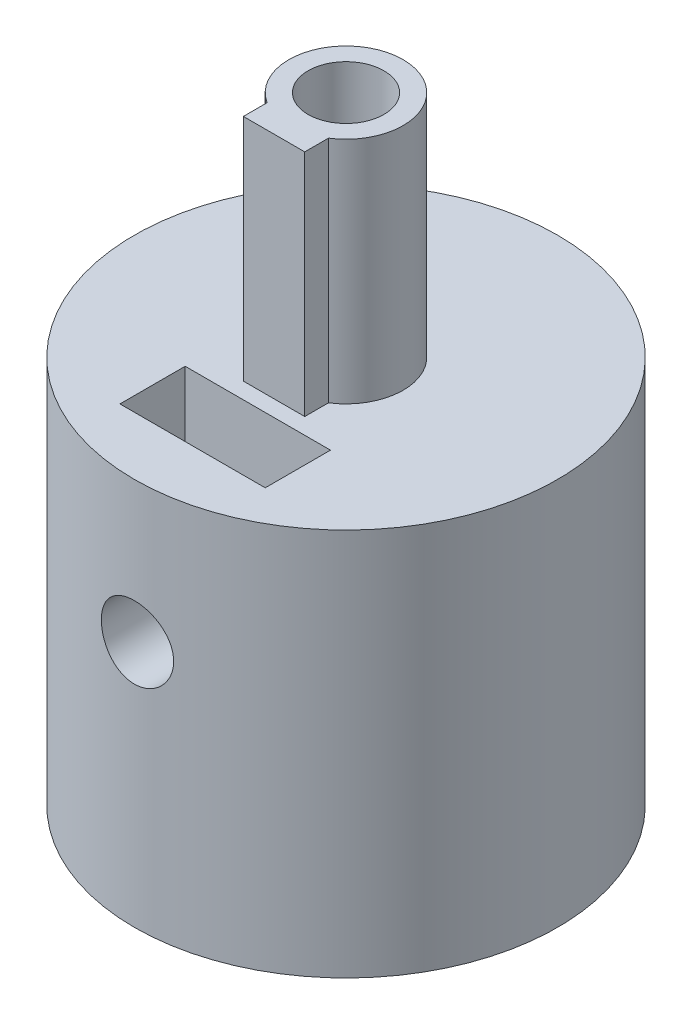
SolidWorks part; units mm, degrees
ref_plane "Front Plane" through (0, 0, 0) normal (0, 0, 1) x (1, 0, 0)
ref_plane "Top Plane" through (0, 0, 0) normal (0, 1, 0) x (1, 0, 0)
ref_plane "Right Plane" through (0, 0, 0) normal (1, 0, 0) x (0, 0, -1)
sketch "Sketch1" plane through (0, 0, 0) normal (0, 1, 0) x (1, 0, 0)
  circle A0 centre (0, 0) radius 1.965 construction
  circle A1 centre (0, 0) radius 6
  dimension "D1" = 3.93
  dimension "D2" = 12
extrude "Boss-Extrude1" add sketch "Sketch1" along normal blind 10
sketch "Sketch2" plane through (0, 0, 0) normal (0, 0, 1) x (1, 0, 0)
  line L0 (0, 10) -> (0, 0) construction
  line L1 (6, 10) -> (-6, 10) construction
  circle A0 centre (0, 7) radius 1.025
  dimension "D1" = 2.05
  dimension "D2" = 3
extrude "Cut-Extrude1" cut sketch "Sketch2" along normal through all
sketch "Sketch4" plane through (0, 0, 0) normal (0, 1, 0) x (1, 0, 0)
  circle A0 centre (0, 0) radius 2.1
  dimension "D1" = 4.2
extrude "Cut-Extrude4" cut sketch "Sketch4" along normal through all
sketch "Sketch5" plane through (0, 10, 0) normal (0, 1, 0) x (1, 0, 0)
  line L0 (-6, 0) -> (6, 0) construction
  line L2 (-0.475, -3.5346) -> (0.475, -3.5346)
  line L3 (-0.475, -3.5346) -> (-0.475, 3.5346)
  line L4 (-0.475, 3.5346) -> (0.475, 3.5346)
  line L5 (0.475, -3.5346) -> (0.475, 3.5346)
  line L6 (0, 3.5346) -> (0, -3.5346) construction
  line L7 (-0.475, 0) -> (0.475, 0) construction
  circle A0 centre (0, 0) radius 6 construction
  point P5 (0, 0)
  dimension "D1" = 0.95
extrude "Boss-Extrude2" add sketch "Sketch5" against normal blind 1.2
sketch "Sketch7" plane through (0, 10, 0) normal (0, 1, 0) x (1, 0, 0)
  circle A0 centre (0, 0) radius 6
  circle A1 centre (0, 0) radius 6 construction
extrude "Boss-Extrude3" add sketch "Sketch7" along normal blind 1
sketch "Sketch8" plane through (0, 11, 0) normal (0, 1, 0) x (1, 0, 0)
  line L0 (0, 0) -> (0, -6) construction
  line L2 (-0.87, -1.2) -> (0.87, -1.2)
  line L3 (-0.87, -1.2) -> (-0.87, -2.04)
  line L4 (-0.87, -2.04) -> (0.87, -2.04)
  line L5 (0.87, -1.2) -> (0.87, -2.04)
  line L6 (0, -2.04) -> (0, -1.2) construction
  line L7 (-0.87, -1.62) -> (0.87, -1.62) construction
  circle A0 centre (0, 0) radius 1.62
  circle A1 centre (0, 0) radius 6 construction
  point P3 (0, -1.62)
  dimension "D1" = 3.24
  dimension "D2" = 2.04
  dimension "D3" = 1.74
extrude "Boss-Extrude4" add sketch "Sketch8" along normal blind 6.5 contours A0 L3 L4 L5
sketch "Sketch9" plane through (0, 17.5, 0) normal (0, 1, 0) x (1, 0, 0)
  circle A0 centre (0, 0) radius 1.075
  dimension "D1" = 2.15
extrude "Cut-Extrude5" cut sketch "Sketch9" against normal blind 6
sketch "Sketch3" plane through (0, 0, 0) normal (0, 0, 1) x (1, 0, 0)
  line L1 (0, 4.6213) -> (2.06, 5.8107)
  line L2 (2.06, 5.8107) -> (2.06, 8.1893)
  line L3 (2.06, 8.1893) -> (0, 9.3787) construction
  line L4 (0, 9.3787) -> (-2.06, 8.1893) construction
  line L5 (-2.06, 8.1893) -> (-2.06, 5.8107)
  line L6 (-2.06, 5.8107) -> (0, 4.6213)
  line L10 (-2.06, 8.1893) -> (2.06, 8.1893) construction
  line L11 (-2.06, 8.1893) -> (-2.06, 11.3631)
  line L12 (2.06, 8.1893) -> (2.06, 11.3631)
  line L13 (-2.06, 11.3631) -> (2.06, 11.3631)
  circle A0 centre (0, 7) radius 2.06 construction
  dimension "D1" = 4.12
extrude "Cut-Extrude2" cut sketch "Sketch3" along normal blind 1.85 from offset 2.5
